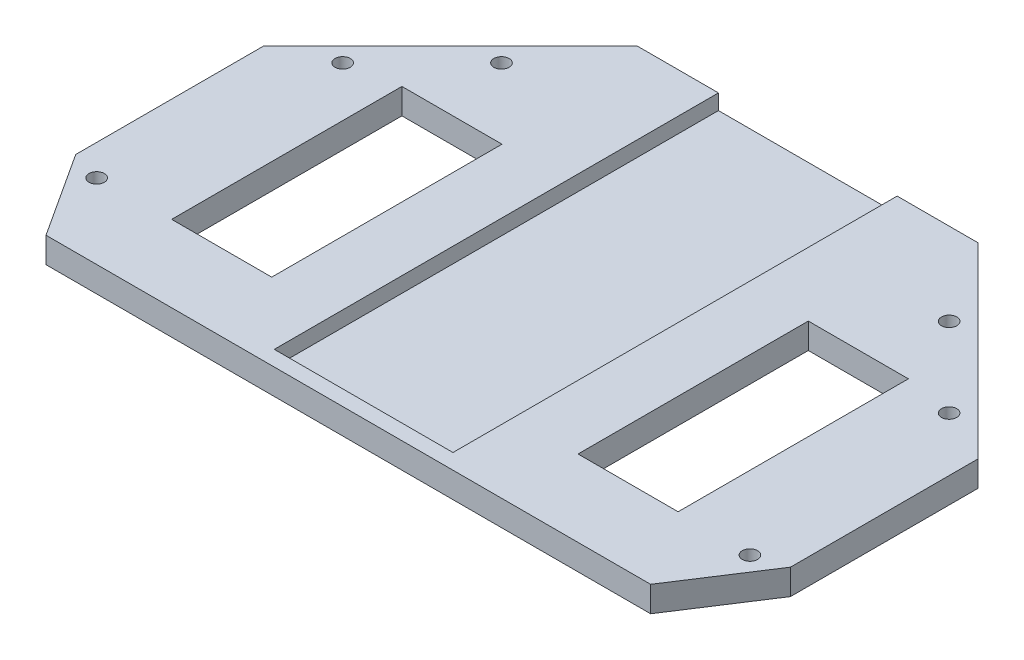
SolidWorks part; units mm, degrees
ref_plane "Front Plane" through (0, 0, 0) normal (0, 0, 1) x (1, 0, 0)
ref_plane "Top Plane" through (0, 0, 0) normal (0, 1, 0) x (1, 0, 0)
ref_plane "Right Plane" through (0, 0, 0) normal (1, 0, 0) x (0, 0, -1)
sketch "Sketch1" plane through (0, 0, 0) normal (0, 1, 0) x (1, 0, 0)
  line L0 (-59.2137, -30) -> (-70, -13.3906)
  line L1 (-70, -13.3906) -> (-70, 23.3381)
  line L2 (-70, 23.3381) -> (-33.3381, 60)
  line L4 (0, -30) -> (0, 60)
  line L5 (0, -30) -> (-59.2137, -30)
  line L6 (-59.397, 28.2843) -> (-43.8406, 43.8406) construction
  line L7 (-51.9976, -33.7676) -> (-63.9796, -15.3169) construction
  line L8 (-33.3381, 60) -> (0, 60)
  line L9 (0, 0) -> (-85, 0) construction
  line L10 (-43.8406, 43.8406) -> (0, 0) construction
  line L11 (-51.9976, -33.7676) -> (0, 0) construction
  line L12 (-49.6, 30.1) -> (-30, 30.1)
  line L13 (-49.6, 30.1) -> (-49.6, -15)
  line L14 (-49.6, -15) -> (-30, -15)
  line L15 (-30, 30.1) -> (-30, -15)
  circle A0 centre (0, 0) radius 85 construction
  circle A1 centre (-43.8406, 43.8406) radius 1.5
  circle A2 centre (-59.397, 28.2843) radius 1.5
  circle A4 centre (-63.9796, -15.3169) radius 1.5
  dimension "D7" = 3
  dimension "D17" = 170
  dimension "D2" = 60
  dimension "D3" = 4
  dimension "D5" = 30
  dimension "D6" = 70
  dimension "D8" = 62
  dimension "D9" = 22
  dimension "D10" = 22
  dimension "D11" = 19.6
  dimension "D12" = 45.1
  dimension "D13" = 30
  dimension "D14" = 45
  dimension "D15" = 33
  dimension "D16" = 15
  dimension "D18" = 4
extrude "Boss-Extrude1" add sketch "Sketch1" along normal blind 5
mirror "Mirror1" about plane through (0, 5, 30) normal (-1, 0, 0) of "Boss-Extrude1"
sketch "Sketch2" plane through (0, 5, 0) normal (0, 1, 0) x (1, 0, 0)
  line L0 (33.3381, 60) -> (-33.3381, 60) construction
  line L1 (-17.5, 60) -> (17.5, 60)
  line L2 (-17.5, 60) -> (-17.5, -27)
  line L3 (-17.5, -27) -> (17.5, -27)
  line L4 (17.5, 60) -> (17.5, -27)
  line L5 (-59.2137, -30) -> (59.2137, -30) construction
  dimension "D1" = 3
  dimension "D2" = 35
  dimension "D3" = 17.5
extrude "Cut-Extrude1" cut sketch "Sketch2" against normal blind 3
